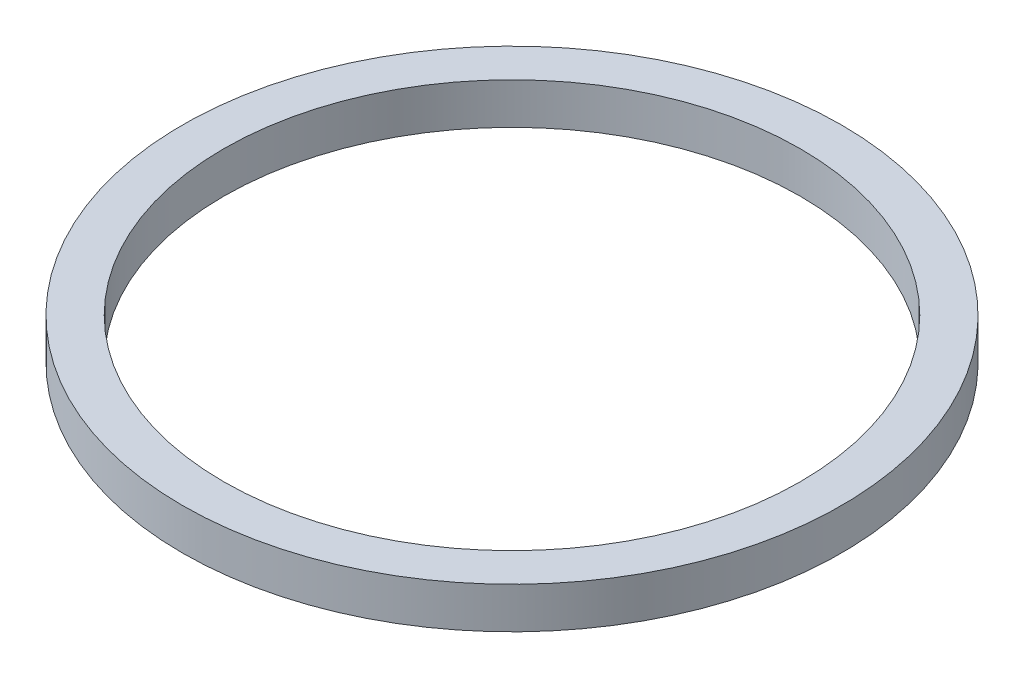
SolidWorks part; units mm, degrees
ref_plane "Front Plane" through (0, 0, 0) normal (0, 0, 1) x (1, 0, 0)
ref_plane "Top Plane" through (0, 0, 0) normal (0, 1, 0) x (1, 0, 0)
ref_plane "Right Plane" through (0, 0, 0) normal (1, 0, 0) x (0, 0, -1)
sketch "Sketch1" plane through (0, 0, 0) normal (0, 1, 0) x (1, 0, 0)
  circle A0 centre (0, 0) radius 35
  circle A1 centre (0, 0) radius 40
  dimension "D1" = 70
  dimension "D2" = 80
extrude "Boss-Extrude1" add sketch "Sketch1" along normal blind 5
